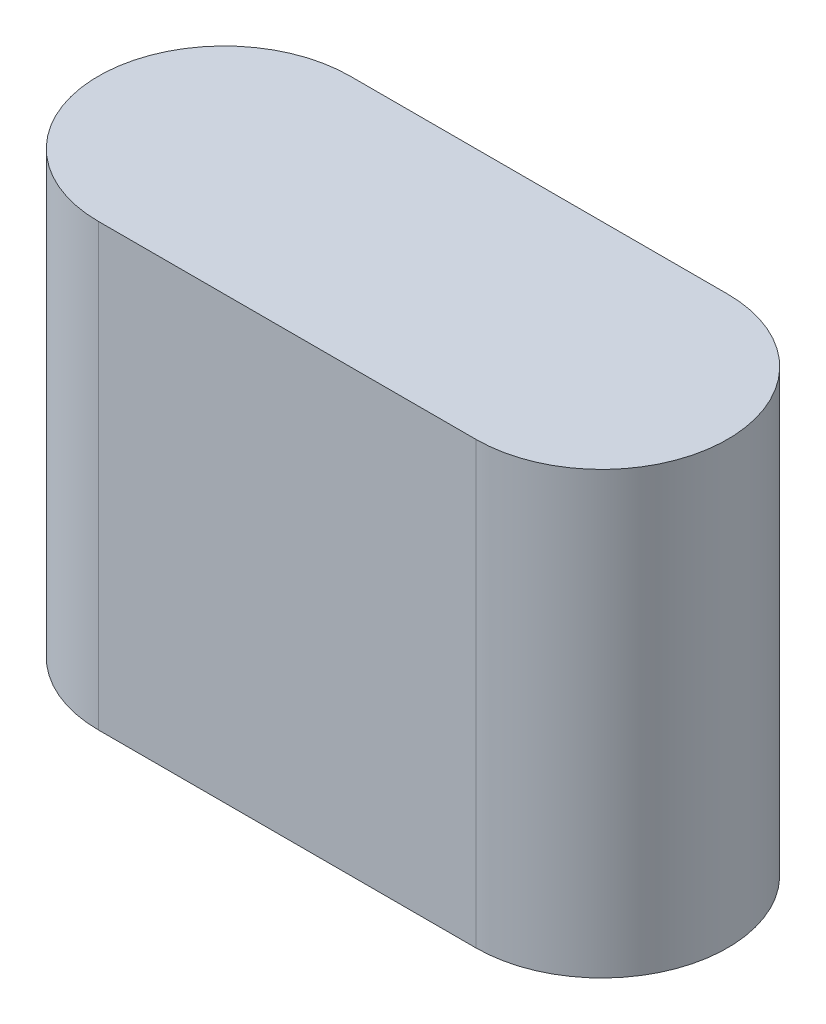
SolidWorks part; units mm, degrees
ref_plane "정면" through (0, 0, 0) normal (0, 0, 1) x (1, 0, 0)
ref_plane "윗면" through (0, 0, 0) normal (0, 1, 0) x (1, 0, 0)
ref_plane "우측면" through (0, 0, 0) normal (1, 0, 0) x (0, 0, -1)
sketch "스케치1" plane through (0, 0, 0) normal (0, 1, 0) x (1, 0, 0)
  line L0 (-82.3431, 0) -> (87.7406, 0) construction
  line L1 (0, 59.1841) -> (0, -58.431) construction
  line L2 (-11.9247, 0) -> (18.0753, 0) construction
  line L3 (-11.9247, 10) -> (18.0753, 10)
  line L4 (-11.9247, -10) -> (18.0753, -10)
  arc A0 (-11.9247, 10) -> (-11.9247, -10) centre (-11.9247, 0) ccw
  arc A1 (18.0753, -10) -> (18.0753, 10) centre (18.0753, 0) ccw
  point P7 (3.0753, 0)
  dimension "D2" = 10
  dimension "D1" = 30
extrude "보스-돌출1" add sketch "스케치1" along normal blind 35
